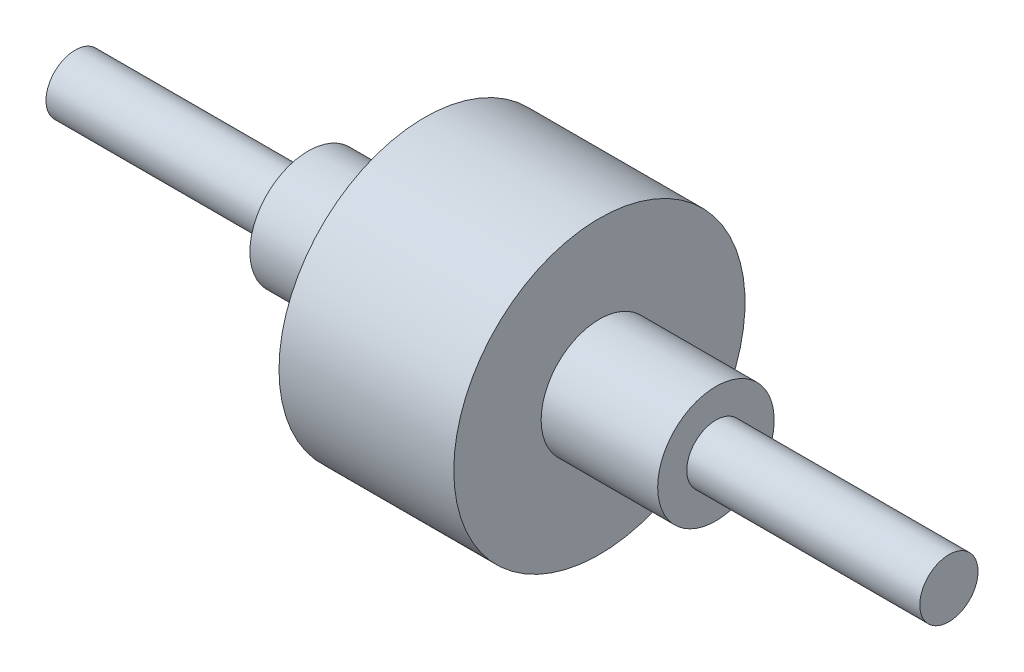
SolidWorks part; units mm, degrees
ref_plane "Alzado" through (0, 0, 0) normal (0, 0, 1) x (1, 0, 0)
ref_plane "Planta" through (0, 0, 0) normal (0, 1, 0) x (1, 0, 0)
ref_plane "Vista lateral" through (0, 0, 0) normal (1, 0, 0) x (0, 0, -1)
sketch "Croquis1" plane through (0, 0, 0) normal (0, 0, 1) x (1, 0, 0)
  line L0 (0, 0) -> (150, 0) construction
  line L1 (0, 0) -> (0, 50) construction
  line L2 (150, 0) -> (150, 10)
  line L3 (150, 10) -> (70, 10)
  line L4 (70, 10) -> (70, 20)
  line L5 (70, 20) -> (30, 20)
  line L6 (30, 20) -> (30, 50)
  line L7 (30, 50) -> (-30, 50)
  line L8 (-150, 0) -> (-150, 10)
  line L9 (-150, 10) -> (-70, 10)
  line L10 (-70, 10) -> (-70, 20)
  line L11 (-70, 20) -> (-30, 20)
  line L12 (-30, 20) -> (-30, 50)
  line L13 (-150, 0) -> (150, 0)
  dimension "D1" = 10
  dimension "D2" = 20
  dimension "D3" = 50
  dimension "D4" = 80
  dimension "D5" = 150
  dimension "D6" = 40
revolve "Revolución5" add sketch "Croquis1" angle 360 about L13
equation "\"A\"= 10mm"
equation "\"D6@Croquis1\"=\"A\"*4"
equation "\"D1@Croquis1\"=\"A\""
equation "\"D4@Croquis1\"=\"D6@Croquis1\"*2"
equation "\"D2@Croquis1\"=\"D1@Croquis1\"*2"
equation "\"D3@Croquis1\"=\"A\"*5"
equation "\"D5@Croquis1\"=\"D3@Croquis1\"*3"
